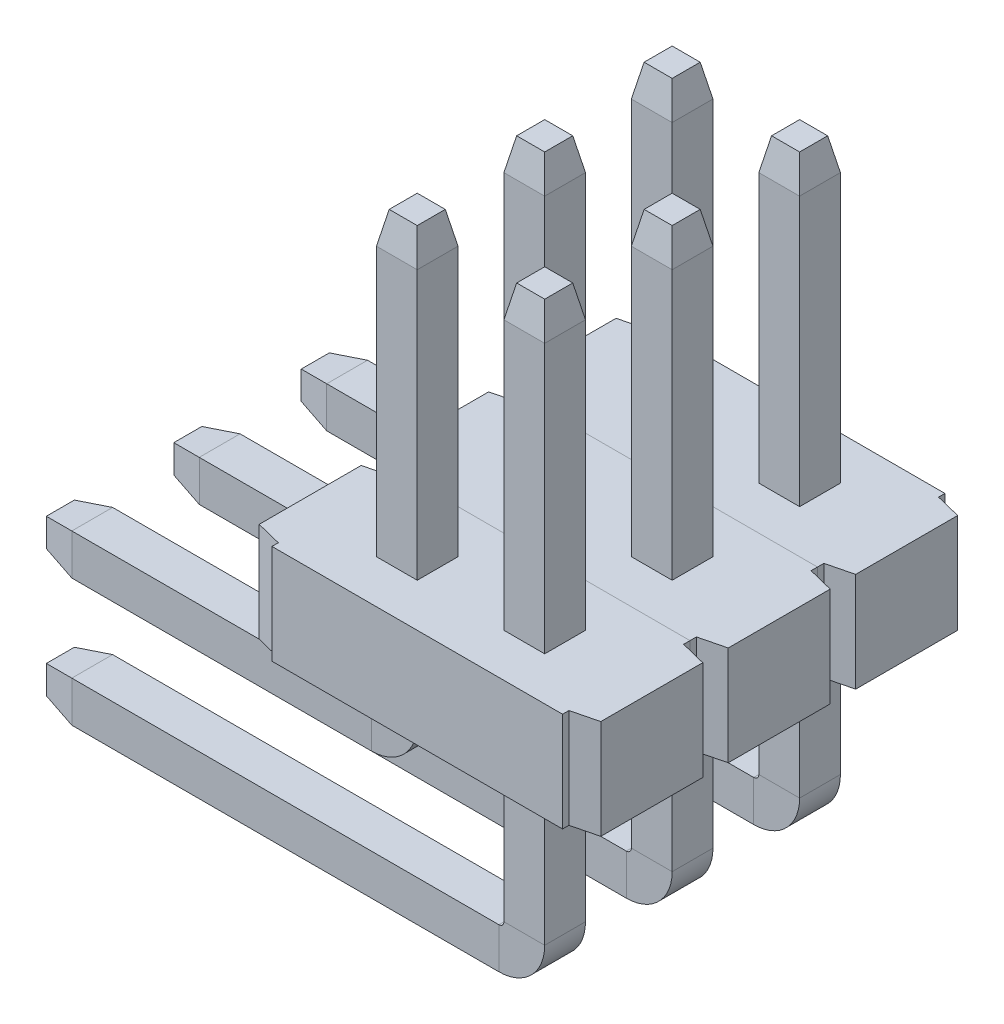
SolidWorks part; units mm, degrees
ref_plane "Front Plane" through (0, 0, 0) normal (0, 0, 1) x (1, 0, 0)
ref_plane "Top Plane" through (0, 0, 0) normal (0, 1, 0) x (1, 0, 0)
ref_plane "Right Plane" through (0, 0, 0) normal (1, 0, 0) x (0, 0, -1)
sketch "Sketch1" plane through (0, 0, 0) normal (0, 1, 0) x (1, 0, 0)
  line L0 (-1.7018, -0.508) -> (-1.4478, -0.5715)
  line L2 (-1.7018, -0.508) -> (-1.7018, 0.508)
  line L4 (1.7018, -0.508) -> (1.7018, 0.508)
  line L5 (-1.4478, 0.5715) -> (-1.4478, 0.635)
  line L6 (-1.4478, 0.635) -> (1.4478, 0.635)
  line L7 (1.4478, -0.5715) -> (1.7018, -0.508)
  line L8 (-1.7018, 0.508) -> (-1.4478, 0.5715)
  line L9 (1.4478, 0.5715) -> (1.7018, 0.508)
  line L10 (1.4478, 0.635) -> (1.4478, 0.5715)
  line L12 (-55, 0) -> (55, 0) construction
  line L13 (1.4478, -0.635) -> (1.4478, -0.5715)
  line L14 (-1.4478, -0.5715) -> (-1.4478, -0.635)
  line L15 (-1.4478, -0.635) -> (1.4478, -0.635)
  point P0 (0, 0)
  point P1 (0, -0.635)
  dimension "D1" = 1.27
  dimension "D2" = 3.4036
  dimension "D3" = 0.254
  dimension "D4" = 0.127
  dimension "D5" = 0.0635
extrude "Boss-Extrude2" add sketch "Sketch1" along normal blind 0.9906
sketch "Sketch2" plane through (0, 0, 0) normal (0, 0, 1) x (1, 0, 0)
  line L0 (-0.635, 0.9906) -> (-0.635, 3.9878)
  line L1 (0, -0.5448) -> (0, 0.5448) construction
  line L2 (0.635, 0.9906) -> (0.635, 3.9878)
  line L3 (-0.635, 0.9906) -> (-0.635, -0.254)
  line L4 (-0.889, -0.508) -> (-4.191, -0.508)
  line L5 (0.635, 0.9906) -> (0.635, -1.524)
  line L6 (0.381, -1.778) -> (-4.191, -1.778)
  line L8 (-1.4478, 0) -> (1.4478, 0) construction
  line L9 (1.4478, 0.9906) -> (-1.4478, 0.9906) construction
  arc A0 (0.635, -1.524) -> (0.381, -1.778) centre (0.381, -1.524) cw
  arc A1 (-0.635, -0.254) -> (-0.889, -0.508) centre (-0.889, -0.254) cw
  dimension "D6" = 0.254
  dimension "D1" = 1.27
  dimension "D2" = 2.9972
  dimension "D3" = 1.27
  dimension "D4" = 2.4892
  dimension "D5" = 0.508
ref_plane "Plane1" through (0, 3.9878, 0) normal (0, 1, 0) x (1, 0, 0)
sketch "Sketch3" plane through (0, 3.9878, 0) normal (0, 1, 0) x (1, 0, 0)
  line L0 (0, -0.5448) -> (0, 0.5448) construction
  line L1 (-0.8382, -0.2032) -> (-0.4318, -0.2032)
  line L2 (-0.8382, -0.2032) -> (-0.8382, 0.2032)
  line L3 (-0.8382, 0.2032) -> (-0.4318, 0.2032)
  line L4 (-0.4318, -0.2032) -> (-0.4318, 0.2032)
  line L5 (-0.8382, -0.2032) -> (-0.4318, 0.2032) construction
  line L6 (-0.8382, 0.2032) -> (-0.4318, -0.2032) construction
  line L7 (0.8382, 0.2032) -> (0.4318, -0.2032) construction
  line L8 (0.8382, -0.2032) -> (0.4318, 0.2032) construction
  line L9 (0.4318, -0.2032) -> (0.4318, 0.2032)
  line L10 (0.8382, 0.2032) -> (0.4318, 0.2032)
  line L11 (0.8382, -0.2032) -> (0.8382, 0.2032)
  line L12 (0.8382, -0.2032) -> (0.4318, -0.2032)
  point P0 (-0.635, 0)
  point P12 (0.635, 0)
  dimension "D1" = 0.4064
sketch "Sketch5" plane through (0, 3.9878, 0) normal (0, 1, 0) x (1, 0, 0)
  line L0 (-0.8382, 0.2032) -> (-0.4318, 0.2032) construction
  line L1 (-0.4318, -0.2032) -> (-0.4318, 0.2032) construction
  line L2 (-0.8382, -0.2032) -> (-0.4318, -0.2032) construction
  line L4 (-0.8382, 0.2032) -> (-0.4318, 0.2032)
  line L5 (-0.4318, -0.2032) -> (-0.4318, 0.2032)
  line L6 (-0.8382, -0.2032) -> (-0.4318, -0.2032)
  line L7 (-0.8382, -0.2032) -> (-0.8382, 0.2032)
sketch "Sketch6" plane through (0, 3.9878, 0) normal (0, 1, 0) x (1, 0, 0)
  line L0 (0.8382, 0.2032) -> (0.4318, 0.2032) construction
  line L1 (0.8382, -0.2032) -> (0.8382, 0.2032) construction
  line L2 (0.8382, -0.2032) -> (0.4318, -0.2032) construction
  line L3 (0.4318, -0.2032) -> (0.4318, 0.2032) construction
  line L4 (0.8382, 0.2032) -> (0.4318, 0.2032)
  line L5 (0.8382, -0.2032) -> (0.8382, 0.2032)
  line L6 (0.8382, -0.2032) -> (0.4318, -0.2032)
  line L7 (0.4318, -0.2032) -> (0.4318, 0.2032)
sweep "Sweep5" add profiles "Sketch5" path "Sketch2"
sketch "Sketch7" plane through (0, 0, 0) normal (0, 0, 1) x (1, 0, 0)
  line L0 (0.381, -1.778) -> (-4.191, -1.778) construction
  line L1 (0.635, 0.9906) -> (0.635, -1.524) construction
  line L2 (0.635, 0.9906) -> (0.635, 3.9878) construction
  line L3 (0.381, -1.778) -> (-4.191, -1.778)
  line L4 (0.635, 0.9906) -> (0.635, -1.524)
  line L5 (0.635, 0.9906) -> (0.635, 3.9878)
  arc A0 (0.381, -1.778) -> (0.635, -1.524) centre (0.381, -1.524) ccw construction
  arc A1 (0.381, -1.778) -> (0.635, -1.524) centre (0.381, -1.524) ccw
sweep "Sweep6" add profiles "Sketch6" path "Sketch7"
chamfer "Chamfer1" distance 0.0635 distance2 0.3175 8 edges at (-4.191, -1.778, -0.2032) (-4.191, -1.5748, 0) (-4.191, -1.778, 0.2032) (-4.191, -1.9812, 0) (-0.4318, 3.9878, 0) (-0.635, 3.9878, 0.2032) (-0.8382, 3.9878, 0) (-0.635, 3.9878, -0.2032)
chamfer "Chamfer2" distance 0.3175 distance2 0.0635 8 edges at (0.635, 3.9878, 0.2032) (0.4318, 3.9878, 0) (0.635, 3.9878, -0.2032) (0.8382, 3.9878, 0) (-4.191, -0.3048, 0) (-4.191, -0.508, 0.2032) (-4.191, -0.7112, 0) (-4.191, -0.508, -0.2032)
pattern_linear "LPattern1" count 3 spacing 1.27 along (0, 0, -1) of bodies 105
ref_plane "Plane2" through (0, 0, -1.27) normal (0, 0, 1) x (1, 0, 0)
sketch "Sketch8" plane through (0, 3.9878, 0) normal (0, 1, 0) x (1, 0, 0)
  point P0 (-0.635, 0)
sketch "Sketch9" plane through (-4.191, 0, 0) normal (-1, 0, 0) x (0, 0, 1)
  point P0 (0, -1.778)
ref_plane "Plane3" through (0, 0, 0) normal (-1, 0, 0) x (0, 0, 1)
